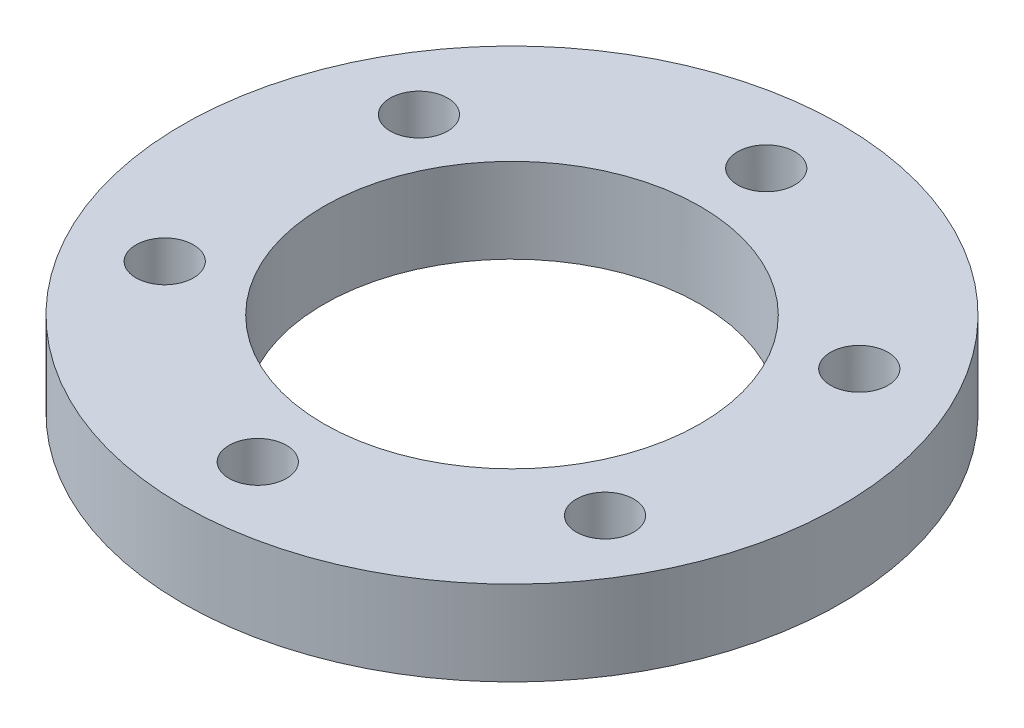
SolidWorks part; units mm, degrees
ref_plane "前视基准面" through (0, 0, 0) normal (0, 0, 1) x (1, 0, 0)
ref_plane "上视基准面" through (0, 0, 0) normal (0, 1, 0) x (1, 0, 0)
ref_plane "右视基准面" through (0, 0, 0) normal (1, 0, 0) x (0, 0, -1)
other "Configuration Table"
sketch "草图1" plane through (0, 0, 0) normal (0, 1, 0) x (1, 0, 0)
  circle A0 centre (0, 0) radius 31.5
  circle A1 centre (0, 0) radius 22.5
  dimension "D1" = 45
  dimension "D2" = 63
extrude "凸台-拉伸1" add sketch "草图1" along normal blind 4.5
sketch "草图2" plane through (0, 4.5, 0) normal (0, 1, 0) x (1, 0, 0)
  circle A0 centre (0, 0) radius 26.25 construction
  circle A1 centre (0, 26.25) radius 2.025
  circle A2 centre (18.5616, 18.5616) radius 2.025
  circle A3 centre (26.25, 0) radius 2.025
  circle A4 centre (18.5616, -18.5616) radius 2.025
  circle A5 centre (0, -26.25) radius 2.025
  circle A6 centre (-18.5616, -18.5616) radius 2.025
  circle A7 centre (-26.25, 0) radius 2.025
  circle A8 centre (-18.5616, 18.5616) radius 2.025
  point P21 (0, 0)
  dimension "D1" = 52.5
  dimension "D2" = 4.05
  dimension "D3" = 8
extrude "切除-拉伸1" cut sketch "草图2" against normal through all both and the other way through all
sketch "草图3" plane through (0, 4.5, 0) normal (0, 1, 0) x (1, 0, 0)
  circle A0 centre (0, 0) radius 22.5
  dimension "D1" = 45
extrude "凸台-拉伸2" add sketch "草图3" against normal up to surface (4.5 mm away) up to face at (0, 0, -24.225)
sketch "草图4" plane through (0, 0, 0) normal (0, -1, 0) x (1, 0, 0)
  circle A0 centre (0, 0) radius 13.5 construction
  circle A1 centre (0, 13.5) radius 1.525
  circle A2 centre (11.6913, 6.75) radius 1.525
  circle A3 centre (11.6913, -6.75) radius 1.525
  circle A4 centre (0, -13.5) radius 1.525
  circle A5 centre (-11.6913, -6.75) radius 1.525
  circle A6 centre (-11.6913, 6.75) radius 1.525
  point P18 (0, 0)
  dimension "D1" = 27
  dimension "D2" = 3.05
  dimension "D3" = 6
extrude "切除-拉伸2" cut sketch "草图4" against normal up to surface (4.5 mm away) up to face at (0, 4.5, -24.225)
sketch "草图5" plane through (0, 0, 0) normal (0, -1, 0) x (1, 0, 0)
  circle A0 centre (0, 0) radius 10
  dimension "D1" = 20
extrude "切除-拉伸3" cut sketch "草图5" against normal up to surface (4.5 mm away) up to face at (0, 4.5, 15.025)
sketch "草图6" plane through (0, 0, 0) normal (0, -1, 0) x (1, 0, 0)
  circle A0 centre (0, 0) radius 17.5
  circle A2 centre (0, 0) radius 31.5
  circle A3 centre (0, 0) radius 31.5
  point P3 (-0.3706, 0)
  dimension "D1" = 35
  dimension "D2" = 0
extrude "切除-拉伸4" cut sketch "草图6" against normal through all
